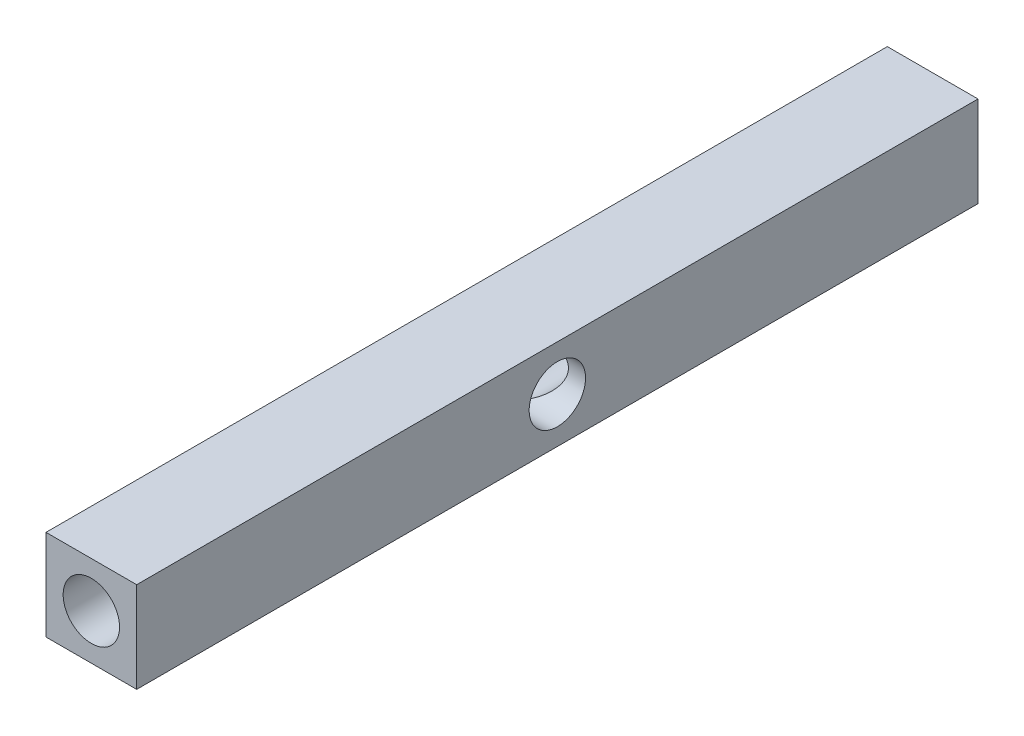
SolidWorks part; units mm, degrees
ref_plane "Plano frontal" through (0, 0, 0) normal (0, 0, 1) x (1, 0, 0)
ref_plane "Plano superior" through (0, 0, 0) normal (0, 1, 0) x (1, 0, 0)
ref_plane "Plano direito" through (0, 0, 0) normal (1, 0, 0) x (0, 0, -1)
sketch "Esboço1" plane through (0, 0, 0) normal (0, 1, 0) x (1, 0, 0)
  line L5 (-2.25, -20.875) -> (2.25, -20.875)
  line L6 (-2.25, -20.875) -> (-2.25, 20.875)
  line L7 (-2.25, 20.875) -> (2.25, 20.875)
  line L8 (2.25, -20.875) -> (2.25, 20.875)
  line L9 (-2.25, -20.875) -> (2.25, 20.875) construction
  line L10 (-2.25, 20.875) -> (2.25, -20.875) construction
  point P0 (0, 0)
  dimension "D1" = 4.5
  dimension "D2" = 41.75
extrude "Ressalto-extrusão1" add sketch "Esboço1" along normal mid plane 4.5
sketch "Esboço2" plane through (0, 0, 20.875) normal (0, 0, 1) x (1, 0, 0)
  circle A0 centre (0, 0) radius 1.4
  dimension "D1" = 2.8
extrude "Corte-extrusão1" cut sketch "Esboço2" against normal through all both and the other way through all
ref_plane "Plano1" through (-2.25, 0, 0) normal (-1, 0, 0) x (0, -1, 0)
sketch "Esboço3" plane through (-2.25, 0, 0) normal (-1, 0, 0) x (0, -1, 0)
  circle A0 centre (0, 0) radius 1.4
  dimension "D1" = 2.8
extrude "Corte-extrusão2" cut sketch "Esboço3" against normal through all both
